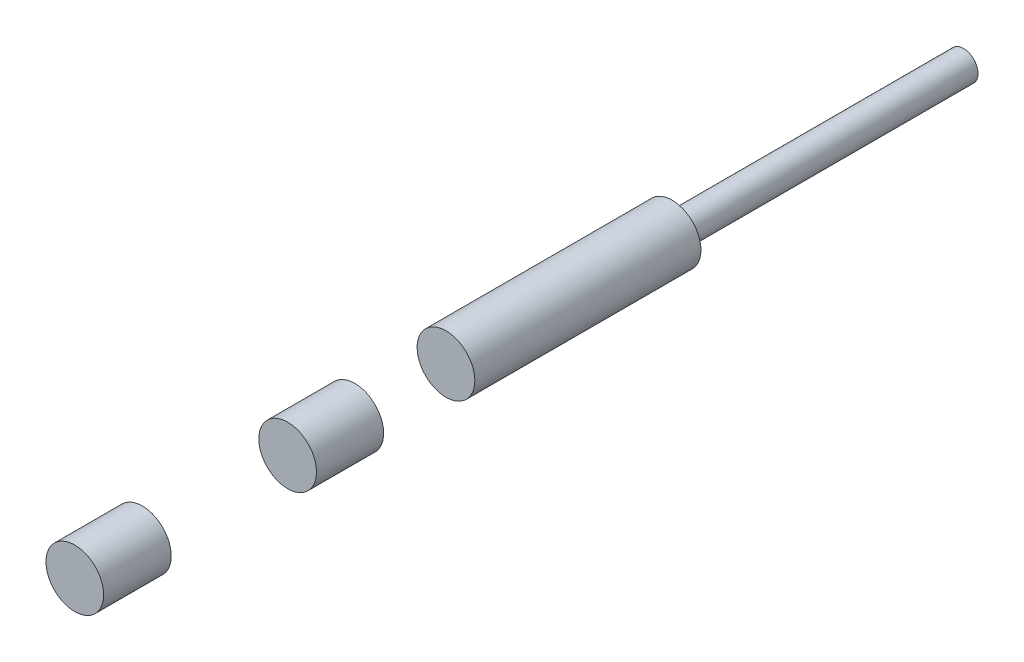
SolidWorks part; units mm, degrees
ref_plane "Ön Düzlem" through (0, 0, 0) normal (0, 0, 1) x (1, 0, 0)
ref_plane "Üst Düzlem" through (0, 0, 0) normal (0, 1, 0) x (1, 0, 0)
ref_plane "Sağ Düzlem" through (0, 0, 0) normal (1, 0, 0) x (0, 0, -1)
sketch "Çizim1" plane through (0, 0, 0) normal (0, 0, 1) x (1, 0, 0)
  circle A0 centre (0, 0) radius 9.9
extrude "Yükseklik-Ekstrüzyon1" add sketch "Çizim1" along normal blind 149 and the other way blind 106
ref_plane "Düzlem1" through (0, 0, -106) normal (0, 0, -1) x (-1, 0, 0)
ref_plane "Düzlem2" through (0, 0, -50.8425) normal (0, 0, -1) x (-1, 0, 0)
sketch "Çizim2" plane through (0, 0, -50.8425) normal (0, 0, -1) x (-1, 0, 0)
  circle A0 centre (0, 0) radius 9.9 construction
  circle A1 centre (0, 0) radius 9.9
ref_plane "Düzlem3" through (0, 0, 149) normal (0, 0, 1) x (1, 0, 0)
ref_plane "Düzlem4" through (0, 0, 94.0962) normal (0, 0, 1) x (1, 0, 0)
sketch "Çizim3" plane through (0, 0, 94.0962) normal (0, 0, 1) x (1, 0, 0)
  circle A0 centre (0, 0) radius 9.9 construction
  circle A1 centre (0, 0) radius 9.9
sketch "Çizim4" plane through (0, 0, -106) normal (0, 0, -1) x (-1, 0, 0)
  circle A0 centre (0, 0) radius 5
  circle A1 centre (0, 0) radius 9.9 construction
  circle A2 centre (0, 0) radius 9.9
extrude "Kes-Ekstrüzyon4" cut sketch "Çizim4" against normal blind 50 contours A0 | A2
sketch "Sketch1" plane through (0, 0, -106) normal (0, 0, -1) x (-1, 0, 0)
  circle A0 centre (0, 0) radius 5
extrude "Boss-Extrude1" add sketch "Sketch1" along normal blind 50
ref_plane "Plane1" through (30, 0, 0) normal (1, 0, 0) x (0, 0, -1)
sketch "Sketch2" plane through (30, 0, 0) normal (1, 0, 0) x (0, 0, -1)
  line L1 (-125.8056, 20.6339) -> (-75.9404, 20.6339)
  line L2 (-125.8056, 20.6339) -> (-125.8056, -24.4167)
  line L3 (-125.8056, -24.4167) -> (-75.9404, -24.4167)
  line L4 (-75.9404, 20.6339) -> (-75.9404, -24.4167)
  line L5 (-52.8992, 20.6339) -> (-21.6045, 20.6339)
  line L6 (-52.8992, 20.6339) -> (-52.8992, -26.4801)
  line L7 (-52.8992, -26.4801) -> (-21.6045, -26.4801)
  line L8 (-21.6045, 20.6339) -> (-21.6045, -26.4801)
extrude "Cut-Extrude1" cut sketch "Sketch2" against normal blind 110
